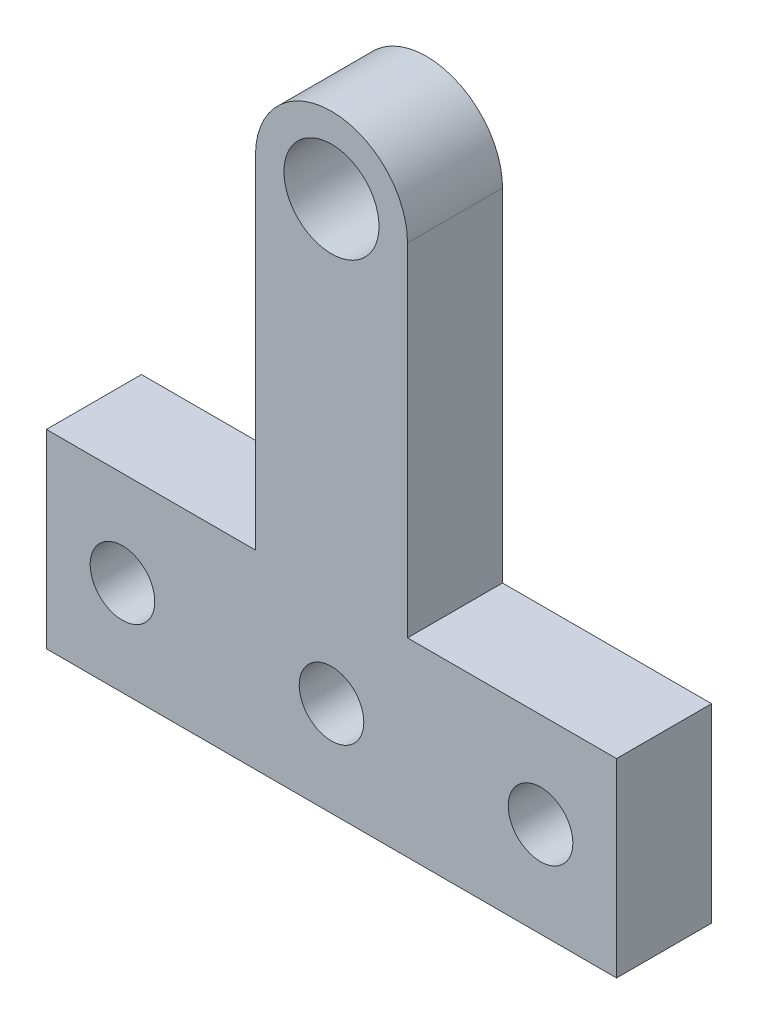
SolidWorks part; units mm, degrees
material "Plain Carbon Steel"
ref_plane "Front Plane" through (0, 0, 0) normal (0, 0, 1) x (1, 0, 0)
ref_plane "Top Plane" through (0, 0, 0) normal (0, 1, 0) x (1, 0, 0)
ref_plane "Right Plane" through (0, 0, 0) normal (1, 0, 0) x (0, 0, -1)
sketch "Sketch1" plane through (0, 0, 0) normal (0, 0, 1) x (1, 0, 0)
  line L1 (0, 0) -> (0, 38.4526) construction
  line L3 (4, 10) -> (4, 28)
  line L4 (-4, 28) -> (-4, 10)
  line L6 (4, 10) -> (15, 10)
  line L7 (15, 10) -> (15, 0)
  line L8 (15, 0) -> (-15, 0)
  line L9 (-15, 0) -> (-15, 10)
  line L10 (-15, 10) -> (-4, 10)
  arc A0 (4, 28) -> (-4, 28) centre (0, 28) ccw
  point P4 (0, 0)
  point P11 (0, 0)
  dimension "D1" = 11
  dimension "D3" = 4
  dimension "D6" = 18
  dimension "D7" = 10
  dimension "D2" = 11
  dimension "D4" = 10
  dimension "D5" = 0
  dimension "D8" = 0
extrude "Boss-Extrude1" add sketch "Sketch1" along normal blind 5
sketch "Sketch2" plane through (0, 0, 5) normal (0, 0, 1) x (1, 0, 0)
  circle A0 centre (0, 28) radius 2.5
  dimension "D1" = 5
extrude "Cut-Extrude1" cut sketch "Sketch2" against normal through all
hole_wizard "CSK for M3 Countersunk Flat Head Screw1" positions "Sketch4" profile "Sketch5" countersink size "M3" standard "ISO" end condition up to next
sketch "Sketch4" plane through (0, 0, 0) normal (0, 0, -1) x (-1, 0, 0)
  line L0 (-15, 0) -> (-15, 10) construction
  line L1 (15, 10) -> (15, 0) construction
  line L3 (15, 0) -> (-15, 0) construction
  point P0 (0, 5)
  point P2 (11, 5)
  point P4 (-11, 5)
  dimension "D1" = 4
  dimension "D2" = 4
  dimension "D3" = 15
  dimension "D4" = 5
  dimension "D5" = 5
  dimension "D6" = 5
sketch "Sketch5" plane through (0, 5, 0) normal (1, 0, 0) x (0, 1, 0)
  line L0 (0, 0) -> (0, 5)
  line L1 (0, 5) -> (1.7, 5)
  line L2 (1.7, 5) -> (1.7, 1.45)
  line L3 (1.7, 1.45) -> (3.15, 0)
  line L5 (3.15, 0) -> (0, 0)
  line L6 (-1.7, 1.45) -> (-3.15, 0) construction
  line L11 (0, -6.35) -> (0, 107.95) construction
  dimension "Thru Hole Dia." = 3.4
  dimension "Thru Hole Depth" = 5
  dimension "Near C'Sink Dia." = 6.3
  dimension "Near C'Sink Angle" = 90
